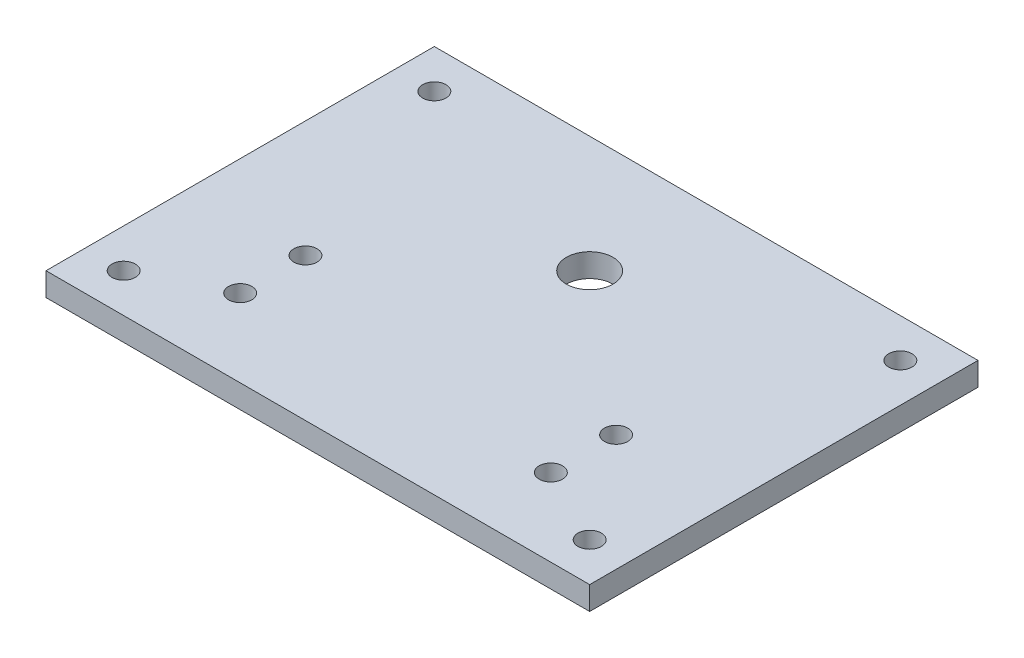
SolidWorks part; units mm, degrees
ref_plane "Ebene vorne" through (0, 0, 0) normal (0, 0, 1) x (1, 0, 0)
ref_plane "Ebene oben" through (0, 0, 0) normal (0, 1, 0) x (1, 0, 0)
ref_plane "Ebene rechts" through (0, 0, 0) normal (1, 0, 0) x (0, 0, -1)
sketch "OutlineRight" plane through (0, 0, 0) normal (1, 0, 0) x (0, 0, -1)
  line L1 (-32.65, 205) -> (-132.65, 205)
  line L2 (-32.65, 205) -> (-32.65, 199)
  line L3 (-32.65, 199) -> (-132.65, 199)
  line L4 (-132.65, 205) -> (-132.65, 199)
sketch "Holes" plane through (0, 0, 0) normal (0, 1, 0) x (1, 0, 0)
  circle A0 centre (0, -62.65) radius 6
  circle A1 centre (-40, -112.65) radius 3
  circle A2 centre (-40, -95.8393) radius 3
  circle A3 centre (40, -95.8393) radius 3
  circle A4 centre (40, -112.65) radius 3
sketch "Skizze3" plane through (0, 0, 0) normal (1, 0, 0) x (0, 0, -1)
  line L1 (-132.65, 205) -> (-32.65, 205)
  line L2 (-132.65, 205) -> (-132.65, 199)
  line L3 (-132.65, 199) -> (-32.65, 199)
  line L4 (-32.65, 205) -> (-32.65, 199)
sketch "Skizze4" plane through (0, 0, 0) normal (0, 1, 0) x (1, 0, 0)
  circle A0 centre (-40, -95.8393) radius 3
  circle A1 centre (-40, -112.65) radius 3
  circle A2 centre (0, -62.65) radius 6
  circle A3 centre (40, -95.8393) radius 3
  circle A4 centre (40, -112.65) radius 3
sketch "OutlineTop" plane through (0, 0, 0) normal (0, 1, 0) x (1, 0, 0)
  line L1 (-70, -132.65) -> (70, -132.65)
  line L2 (-70, -132.65) -> (-70, -32.65)
  line L3 (-70, -32.65) -> (70, -32.65)
  line L4 (70, -132.65) -> (70, -32.65)
  line L5 (-70, -132.65) -> (70, -32.65) construction
  line L6 (-70, -32.65) -> (70, -132.65) construction
  line L8 (-70, -132.65) -> (-50, -132.65)
  line L9 (-70, -132.65) -> (-70, -112.65)
  line L10 (-70, -112.65) -> (-50, -112.65)
  line L11 (-50, -132.65) -> (-50, -112.65)
  line L12 (50, -132.65) -> (50, -112.65)
  line L13 (70, -112.65) -> (50, -112.65)
  line L14 (70, -132.65) -> (70, -112.65)
  line L15 (70, -132.65) -> (50, -132.65)
  line L16 (0, -82.65) -> (44.0576, -82.65) construction
  line L17 (70, -32.65) -> (50, -32.65)
  line L18 (70, -32.65) -> (70, -52.65)
  line L19 (70, -52.65) -> (50, -52.65)
  line L20 (50, -32.65) -> (50, -52.65)
  line L21 (-50, -32.65) -> (-50, -52.65)
  line L22 (-70, -52.65) -> (-50, -52.65)
  line L23 (-70, -32.65) -> (-70, -52.65)
  line L24 (-70, -32.65) -> (-50, -32.65)
  circle A0 centre (-60, -122.65) radius 3
  circle A1 centre (60, -122.65) radius 3
  circle A2 centre (60, -42.65) radius 3
  circle A3 centre (-60, -42.65) radius 3
  point P0 (0, -82.65)
extrude "Aufsatz-Linear austragen2" add sketch "Skizze3" along normal up to vertex (70 mm away) and the other way up to vertex (70 mm away) up to point (70, 0, 132.65) other way up to point (-70, 0, 132.65)
extrude "Schnitt-Linear austragen2" cut sketch "Holes" along normal up to surface (205 mm away) up to face at (0, 205, 82.65)
sketch "Skizze6" plane through (0, 0, 0) normal (0, 1, 0) x (1, 0, 0)
  circle A0 centre (-60, -42.65) radius 3
  circle A1 centre (60, -42.65) radius 3
  circle A2 centre (60, -122.65) radius 3
  circle A3 centre (-60, -122.65) radius 3
extrude "Schnitt-Linear austragen3" cut sketch "Skizze6" along normal up to surface (205 mm away) up to face at (0, 205, 56.65)
